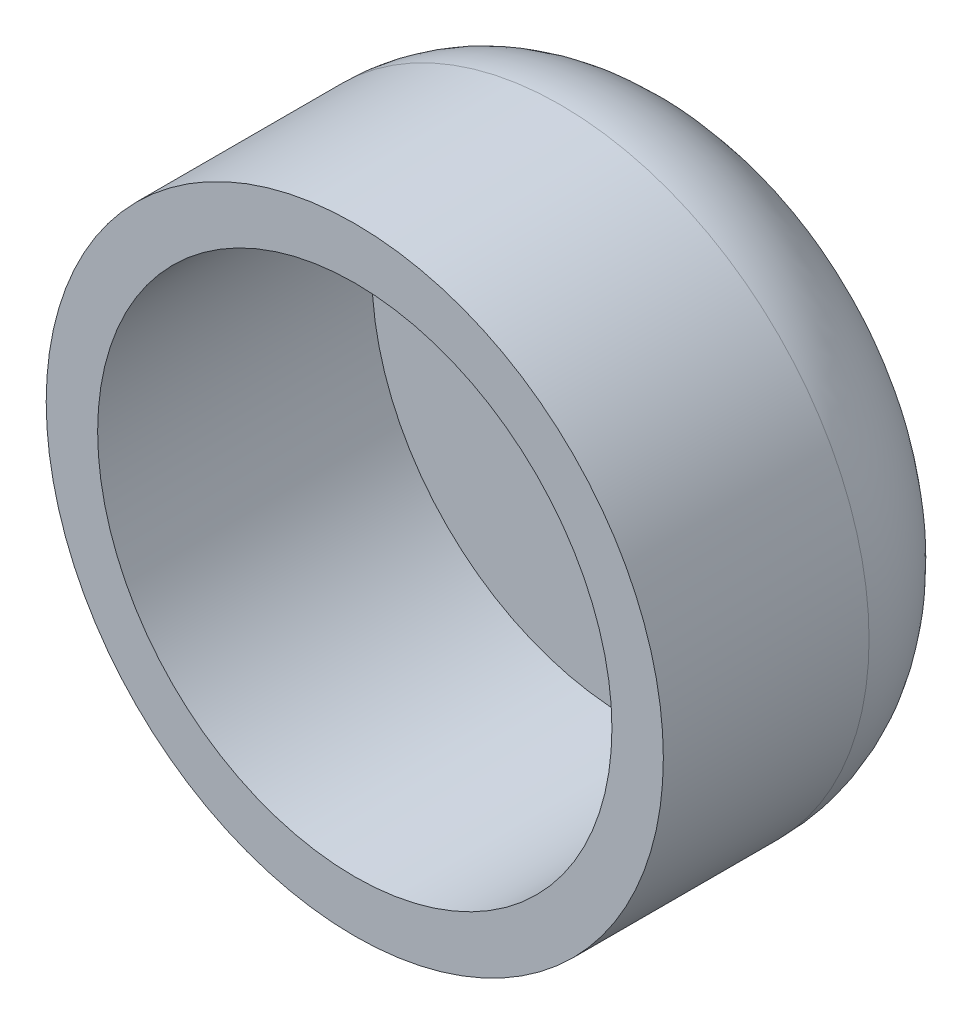
SolidWorks part; units mm, degrees
ref_plane "Front Plane" through (0, 0, 0) normal (0, 0, 1) x (1, 0, 0)
ref_plane "Top Plane" through (0, 0, 0) normal (0, 1, 0) x (1, 0, 0)
ref_plane "Right Plane" through (0, 0, 0) normal (1, 0, 0) x (0, 0, -1)
sketch "Sketch1" plane through (0, 0, 0) normal (0, 0, 1) x (1, 0, 0)
  circle A0 centre (0, 0) radius 0.9
  dimension "D1" = 1.8
extrude "Boss-Extrude1" add sketch "Sketch1" against normal blind 0.5
fillet "Fillet1" radius 0.4 1 edges at (0.9, 0, -0.5)
sketch "Sketch2" plane through (0, 0, 0) normal (0, 0, 1) x (1, 0, 0)
  circle A0 centre (0, 0) radius 0.75
  dimension "D1" = 1.5
extrude "Cut-Extrude1" cut sketch "Sketch2" against normal blind 0.3
sketch "Sketch3" plane through (0, 0, 0) normal (0, 0, 1) x (1, 0, 0)
  circle A1 centre (0, 0) radius 0.9
  circle A2 centre (0, 0) radius 0.9
  circle M2 centre (0, 0) radius 0.75
  circle M3 centre (0, 0) radius 0.9
  dimension "D1" = 0
extrude "Boss-Extrude3" add sketch "Sketch3" along normal blind 0.5 contours M3 M2
